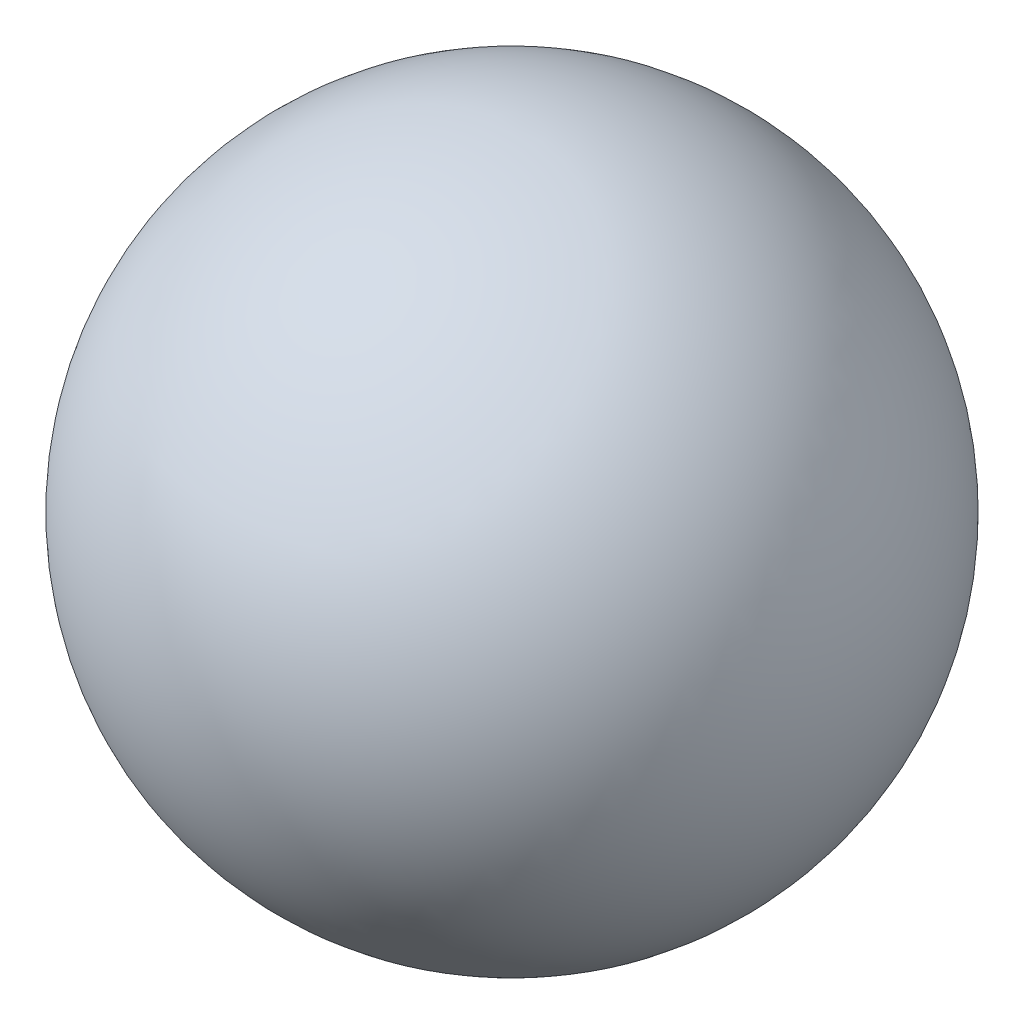
SolidWorks part; units mm, degrees
ref_plane "前基準面" through (0, 0, 0) normal (0, 0, 1) x (1, 0, 0)
ref_plane "上基準面" through (0, 0, 0) normal (0, 1, 0) x (1, 0, 0)
ref_plane "右基準面" through (0, 0, 0) normal (1, 0, 0) x (0, 0, -1)
sketch "草圖1" plane through (0, 0, 0) normal (0, 0, 1) x (1, 0, 0)
  line L0 (0, 0) -> (0, 39)
  arc A0 (0, 39) -> (0, 0) centre (0, 19.5) cw
  dimension "D1" = 19.5
revolve "旋轉1" add sketch "草圖1" angle 360 about L0
